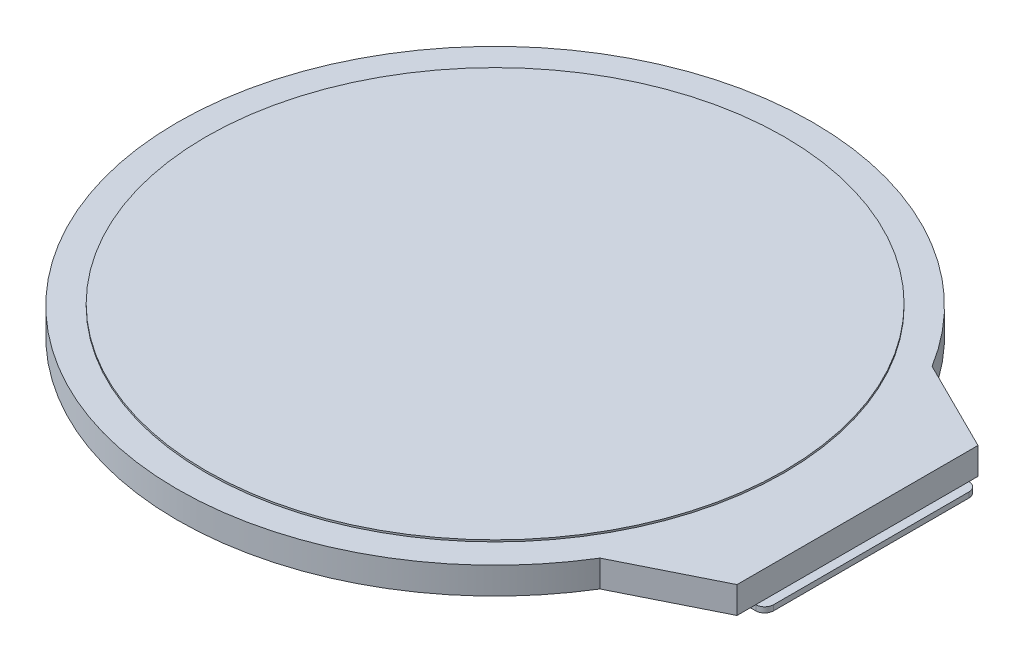
SolidWorks part; units mm, degrees
ref_plane "前视基准面" through (0, 0, 0) normal (0, 0, 1) x (1, 0, 0)
ref_plane "上视基准面" through (0, 0, 0) normal (0, 1, 0) x (1, 0, 0)
ref_plane "右视基准面" through (0, 0, 0) normal (1, 0, 0) x (0, 0, -1)
sketch "草图1" plane through (0, 0, 0) normal (0, 1, 0) x (1, 0, 0)
  line L0 (0, 0) -> (42.2197, 0) construction
  line L1 (20.3, 6.75) -> (20.3, -6.75)
  line L2 (20.3, -6.75) -> (15.1773, -9.3)
  line L3 (20.3, 6.75) -> (15.1773, 9.3)
  line L4 (0, 0) -> (-21.8017, 0) construction
  arc A1 (15.1773, 9.3) -> (15.1773, -9.3) centre (0, 0) ccw
  point P4 (-17.8, 0)
  point P8 (20.3, 0)
  dimension "D1" = 35.6
  dimension "D3" = 38.1
  dimension "D4" = 13.5
  dimension "D5" = 18.6
extrude "凸台-拉伸1" add sketch "草图1" along normal blind 1.5
sketch "草图3" plane through (0, 1.5, 0) normal (0, 1, 0) x (1, 0, 0)
  circle A0 centre (0, 0) radius 16.2
  dimension "D1" = 32.4
extrude "凸台-拉伸2" add sketch "草图3" along normal blind 0.1
sketch "草图4" plane through (0, 0, 0) normal (0, -1, 0) x (1, 0, 0)
  line L0 (0, 0) -> (22.4508, 0) construction
  line L1 (20.8, -6.24) -> (20.8, 5.7)
  line L2 (20.8, 5.7) -> (10.06, 5.7)
  line L3 (10.06, 5.7) -> (10.06, -5.7)
  line L4 (10.06, -5.7) -> (13.26, -5.7)
  line L5 (13.26, -5.7) -> (13.8, -6.24)
  line L6 (13.8, -6.24) -> (20.8, -6.24)
  line L7 (20.3, 6.75) -> (20.3, -6.75) construction
  text T0 "1" font "黑体" height 1
  text T1 "12" font "黑体" height 1
  dimension "D1" = 10.24
  dimension "D2" = 0.5
  dimension "D3" = 135
  dimension "D4" = 11.4
  dimension "D5" = 3.2
  dimension "D6" = 7
extrude "凸台-拉伸3" add sketch "草图4" along normal blind 0.3
fillet "圆角1" radius 0.5 4 edges at (10.06, -0.15, -5.7) (10.06, -0.15, 5.7) (20.8, -0.15, 5.7) (20.8, -0.15, -6.24)
